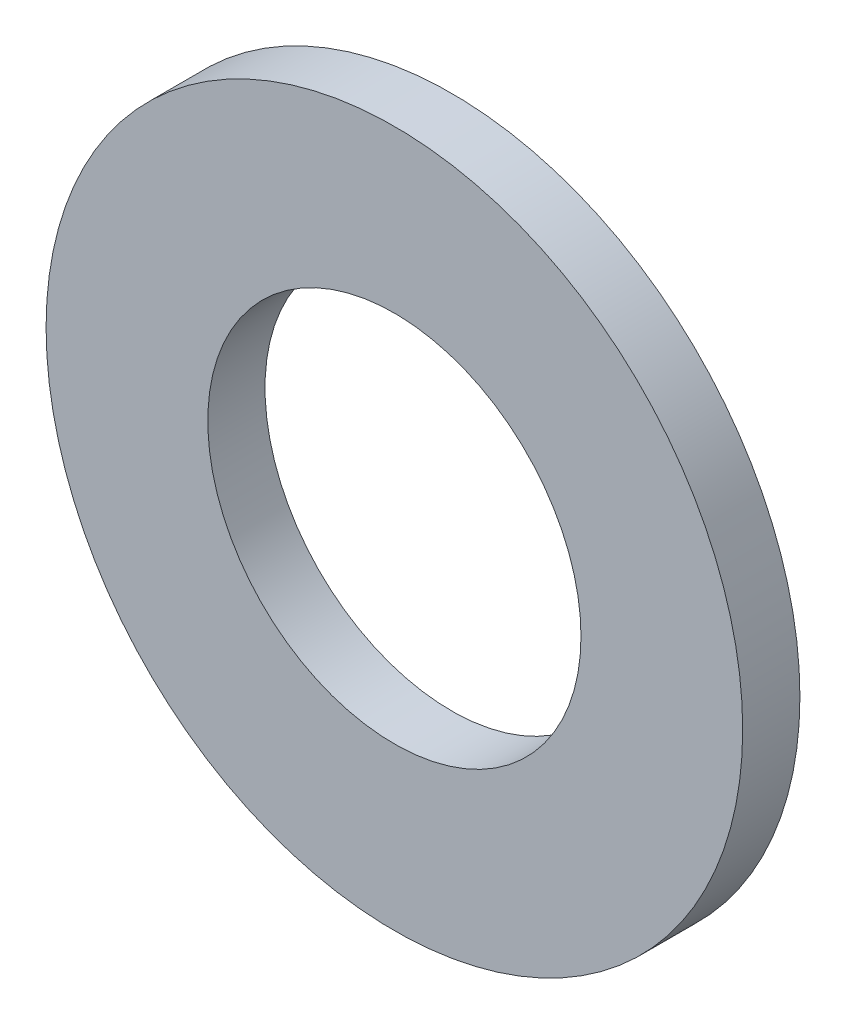
SolidWorks part; units mm, degrees
ref_plane "Front Plane" through (0, 0, 0) normal (0, 0, 1) x (1, 0, 0)
ref_plane "Top Plane" through (0, 0, 0) normal (0, 1, 0) x (1, 0, 0)
ref_plane "Right Plane" through (0, 0, 0) normal (1, 0, 0) x (0, 0, -1)
sketch "Sketch1" plane through (0, 0, 0) normal (0, 0, 1) x (1, 0, 0)
  circle A0 centre (0, 0) radius 7.5
  circle A1 centre (0, 0) radius 14
  dimension "ID" = 15
  dimension "OD" = 28
extrude "Extrude1" add sketch "Sketch1" against normal blind 2.3
